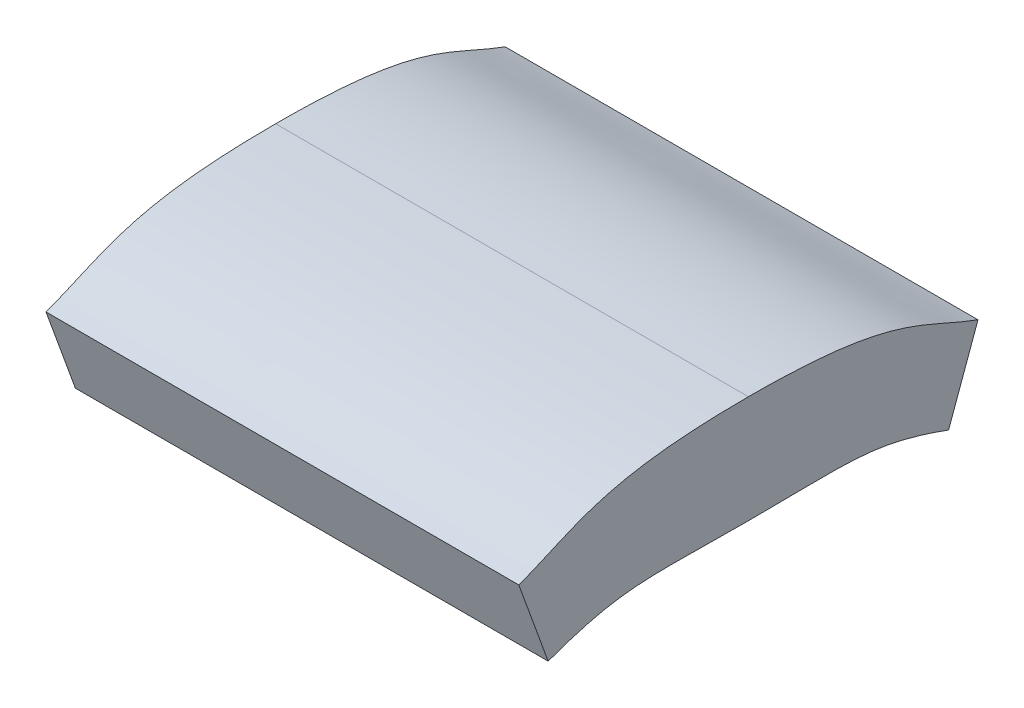
SolidWorks part; units mm, degrees
ref_plane "Front Plane" through (0, 0, 0) normal (0, 0, 1) x (1, 0, 0)
ref_plane "Top Plane" through (0, 0, 0) normal (0, 1, 0) x (1, 0, 0)
ref_plane "Right Plane" through (0, 0, 0) normal (1, 0, 0) x (0, 0, -1)
sketch "Sketch1" plane through (0, 0, 0) normal (1, 0, 0) x (0, 0, -1)
  line L0 (0, 0) -> (0, 10.6913) construction
  line L1 (9.316, -0.9779) -> (10.684, 2.7808)
  line L2 (-4.8433, 0.0221) -> (4.8433, 0.0221) construction
  line L3 (-3.6834, 5.0221) -> (3.6834, 5.0221) construction
  line L4 (8.0087, 3.7546) -> (14.0516, 1.5551) construction
  line L5 (-9.316, -0.9779) -> (-10.684, 2.7808)
  spline S0 degree 3 poles (9.316, -0.9779) (5.7702, 0.3126) (4.6852, 0.0221) (0, 0.0221) knots 0 0 0 0 1 1 1 1
  spline S1 degree 3 poles (10.684, 2.7808) (8.0154, 3.7521) (6.8871, 5.0221) (0, 5.0221) knots 0 0 0 0 1 1 1 1
  spline S2 degree 3 poles (-9.316, -0.9779) (-5.7702, 0.3126) (-4.6852, 0.0221) (0, 0.0221) knots 0 0 0 0 1 1 1 1
  spline S3 degree 3 poles (-10.684, 2.7808) (-8.0154, 3.7521) (-6.8871, 5.0221) (0, 5.0221) knots 0 0 0 0 1 1 1 1
  point P13 (10, 0.9015)
  point P16 (-10, 0.9015)
  dimension "D1" = 4
  dimension "D2" = 20
  dimension "D3" = 1
  dimension "D4" = 20
  dimension "D5" = 5
extrude "Boss-Extrude1" add sketch "Sketch1" along normal blind 22
